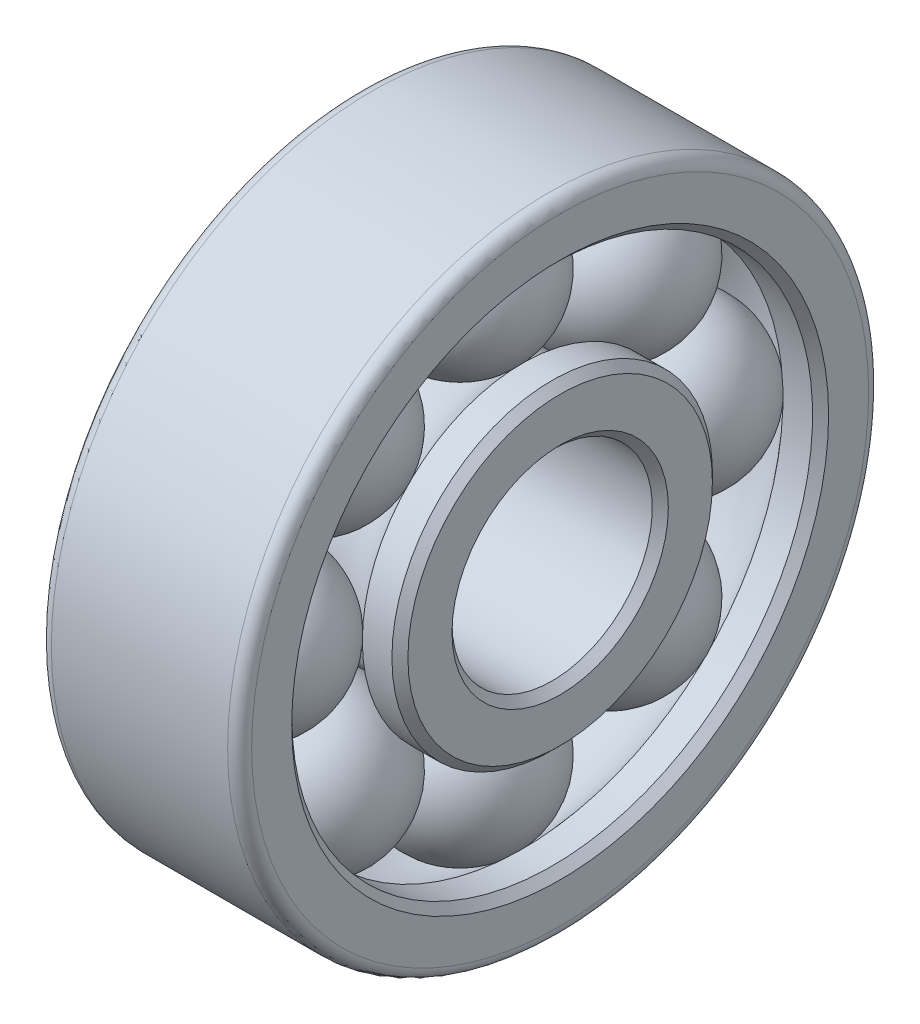
SolidWorks part; units mm, degrees
material "1023 Листовая углеродистая сталь (SS)"
ref_plane "Спереди" through (0, 0, 0) normal (0, 0, 1) x (1, 0, 0)
ref_plane "Сверху" through (0, 0, 0) normal (0, 1, 0) x (1, 0, 0)
ref_plane "Справа" through (0, 0, 0) normal (1, 0, 0) x (0, 0, -1)
sketch "Эскиз1" plane through (0, 0, 0) normal (0, 0, 1) x (1, 0, 0)
  line L0 (-1.0669, -2.5) -> (5.2077, -2.5) construction
  line L1 (0, 0) -> (5, 0)
  line L2 (0, 0) -> (0, 1.5)
  line L3 (0, 1.5) -> (0.9388, 1.5)
  line L4 (5, 0) -> (5, 1.5)
  line L5 (0, 4) -> (0.9388, 4)
  line L6 (0, 4) -> (0, 5.5)
  line L7 (0, 5.5) -> (5, 5.5)
  line L8 (5, 4) -> (5, 5.5)
  line L9 (4.0612, 4) -> (5, 4)
  line L10 (4.0612, 1.5) -> (5, 1.5)
  arc A0 (0.9388, 1.5) -> (4.0612, 1.5) centre (2.5, 2.75) ccw
  arc A1 (4.0612, 4) -> (0.9388, 4) centre (2.5, 2.75) ccw
  dimension "D7" = 1.25
  dimension "D8" = 0
  dimension "D9" = 2
  dimension "D1" = 2.5
  dimension "D2" = 5
  dimension "D3" = 1.5
  dimension "D4" = 5
  dimension "D5" = 1.5
  dimension "D6" = 8
  dimension "D10" = 2.5
revolve "Повернуть1" add sketch "Эскиз1" angle 360 about L0
sketch "Эскиз2" plane through (0, 0, 0) normal (0, 0, 1) x (1, 0, 0)
  line L0 (2.5, 4.75) -> (2.5, 0.75) construction
  line L1 (2.5, 4.75) -> (2.5, 0.75)
  arc A0 (2.5, 4.75) -> (2.5, 0.75) centre (2.5, 2.75) ccw
  arc A1 (0.9388, 1.5) -> (4.0612, 1.5) centre (2.5, 2.75) ccw construction
  dimension "D1" = 2
revolve "Повернуть2" add sketch "Эскиз2" angle 360 about L0
pattern_circular "Круговой массив5" count 8 over 360 about axis through (0, -2.5, 0) along (1, 0, 0) of bodies 105
fillet "Скругление1" radius 0.3 2 edges at (5, -2.5, 8) (0, -2.5, 8)
chamfer "Фаска1" distance 0.2 angle 45 4 edges at (0, -2.5, 2.5) (5, -2.5, 2.5) (5, -2.5, 4) (0, -2.5, 4)
chamfer "Фаска2" distance 0.2 angle 45 2 edges at (5, -2.5, 6.5) (0, -2.5, 6.5)
